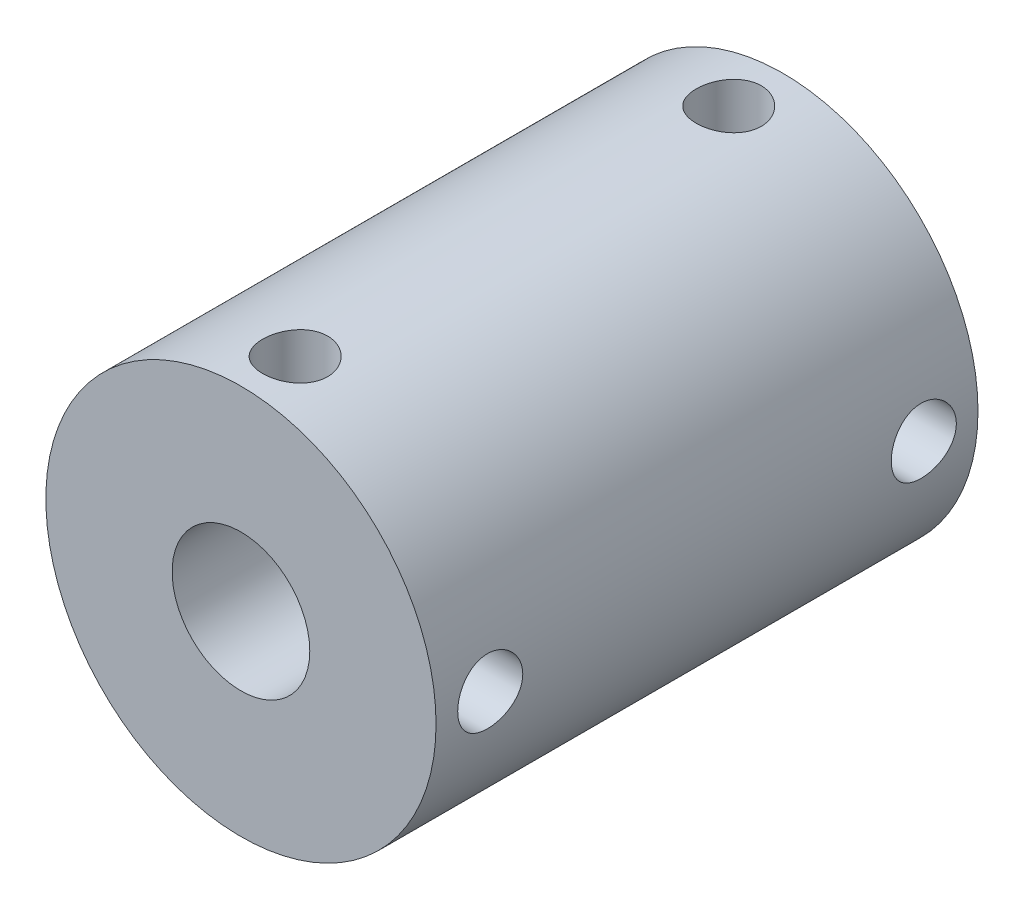
SolidWorks part; units mm, degrees
ref_plane "Front Plane" through (0, 0, 0) normal (0, 0, 1) x (1, 0, 0)
ref_plane "Top Plane" through (0, 0, 0) normal (0, 1, 0) x (1, 0, 0)
ref_plane "Right Plane" through (0, 0, 0) normal (1, 0, 0) x (0, 0, -1)
sketch "Sketch1" plane through (0, 0, 0) normal (0, 0, 1) x (1, 0, 0)
  circle A0 centre (0, 0) radius 9
  dimension "D1" = 18
extrude "Boss-Extrude1" add sketch "Sketch1" along normal mid plane 25
sketch "Sketch2" plane through (0, 0, 12.5) normal (0, 0, 1) x (1, 0, 0)
  circle A0 centre (0, 0) radius 3.175
  dimension "D1" = 6.35
extrude "Cut-Extrude1" cut sketch "Sketch2" against normal through all
sketch "Sketch3" plane through (0, 0, 0) normal (0, 1, 0) x (1, 0, 0)
  circle A0 centre (0, 10) radius 1.5
  circle A1 centre (0, -10) radius 1.5
  dimension "D1" = 3
  dimension "D2" = 3
  dimension "D3" = 10
  dimension "D4" = 10
extrude "Cut-Extrude2" cut sketch "Sketch3" along normal through all
sketch "Sketch4" plane through (0, 0, 0) normal (1, 0, 0) x (0, 0, -1)
  circle A0 centre (-10, 0) radius 1.5
  circle A1 centre (10, 0) radius 1.5
  dimension "D1" = 3
  dimension "D2" = 3
  dimension "D3" = 10
  dimension "D4" = 10
extrude "Cut-Extrude3" cut sketch "Sketch4" along normal through all
